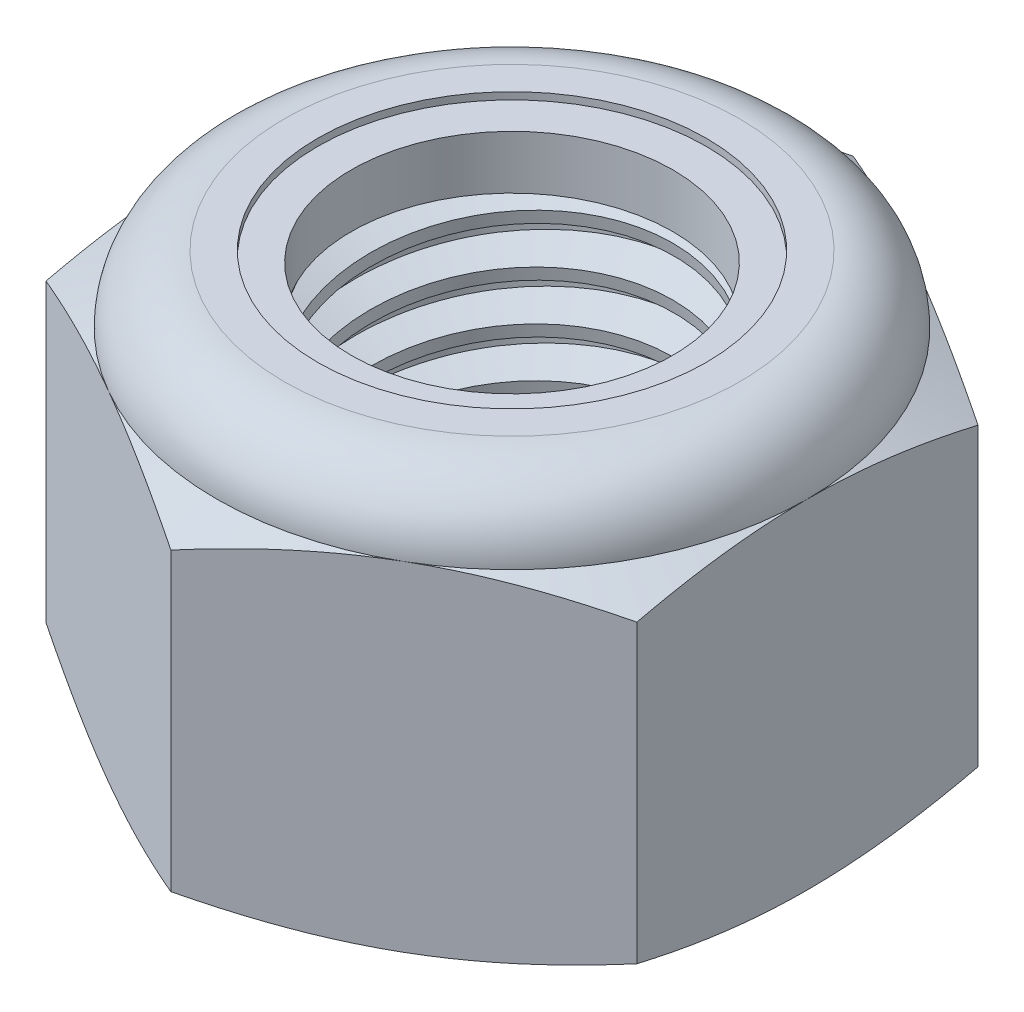
SolidWorks part; units mm, degrees
ref_plane "Front" through (0, 0, 0) normal (0, 0, 1) x (1, 0, 0)
ref_plane "Top" through (0, 0, 0) normal (0, 1, 0) x (1, 0, 0)
ref_plane "Right" through (0, 0, 0) normal (1, 0, 0) x (0, 0, -1)
sketch "Sketch1" plane through (0, 0, 0) normal (0, 1, 0) x (1, 0, 0)
  line L1 (0, 7.3323) -> (-6.35, 3.6662)
  line L2 (-6.35, 3.6662) -> (-6.35, -3.6662)
  line L3 (-6.35, -3.6662) -> (0, -7.3323)
  line L4 (0, -7.3323) -> (6.35, -3.6662)
  line L5 (6.35, -3.6662) -> (6.35, 3.6662)
  line L6 (6.35, 3.6662) -> (0, 7.3323)
  circle A0 centre (0, 0) radius 6.35 construction
  dimension "Hex Flats" = 12.7
extrude "Extrude1" add sketch "Sketch1" along normal blind 8.7312
sketch "Sketch2" plane through (0, 0, 0) normal (1, 0, 0) x (0, 0, -1)
  line L0 (-3.9624, 0) -> (-3.9624, 8.7312) construction
  line L1 (0, 0) -> (3.9624, 0)
  line L2 (0, 0) -> (0, 8.7312)
  line L3 (0, 8.7312) -> (3.9624, 8.7312)
  line L4 (3.9624, 0) -> (3.9624, 8.7312)
  line L5 (-3.6662, 8.7312) -> (3.6662, 8.7312) construction
  line L7 (0, -3.9624) -> (0, 0) construction
  dimension "Thread Dia" = 7.9248
revolve "Revolve1" add sketch "Sketch2" angle 360 about L7
sketch "Sketch3" plane through (0, 0, 0) normal (1, 0, 0) x (0, 0, -1)
  line L0 (3.9624, 8.7312) -> (-3.9624, 8.7312) construction
  line L1 (-3.9624, 8.7312) -> (-3.9624, 7.6729) construction
  line L2 (-3.9624, 7.6729) -> (3.9624, 8.7312) construction
  line L3 (3.9624, 8.7312) -> (3.9799, 8.6001) construction
  line L4 (3.9799, 8.6001) -> (4.1025, 7.6822)
  line L5 (4.1025, 7.6822) -> (3.4909, 7.9342)
  line L6 (3.4909, 7.9342) -> (3.4559, 8.1965)
  line L7 (3.4559, 8.1965) -> (3.9799, 8.6001)
  line L8 (3.4734, 8.0653) -> (4.0412, 8.1412) construction
  line L9 (3.9624, 8.7312) -> (3.9624, 8.1307) construction
  line L10 (3.9624, 8.1307) -> (-3.9624, 7.0723) construction
  line L11 (-3.9624, 7.0723) -> (-3.9624, 7.6729) construction
  line L12 (-0.1509, 8.7312) -> (0.1509, 6.4717) construction
  line L13 (-3.9624, 0) -> (-3.9624, 8.7312) construction
  line L14 (0, 8.7312) -> (3.9624, 8.7312) construction
  line L15 (3.9624, 0) -> (3.9624, 8.7312) construction
  point P13 (0, 7.6015)
  dimension "D1" = 0.1323
  dimension "D2" = 0.2646
  dimension "Thread Pitch" = 1.0583
  dimension "D4" = 60
  dimension "D5" = 1.0583
revolve "Cut-Revolve1" cut sketch "Sketch3" angle 360 about L12
pattern_linear "LPattern1" count 8 spacing 1.0583 along (0, -1, 0) count 2 spacing 1.0583 along (0, 1, 0) of "Cut-Revolve1"
sketch "Sketch4" plane through (0, 0, 0) normal (1, 0, 0) x (0, 0, -1)
  line L0 (0, 8.7312) -> (3.9624, 8.7312)
  line L1 (3.9624, 8.7312) -> (3.4559, 8.4951)
  line L2 (3.4559, 8.4951) -> (3.4559, 0.2362)
  line L3 (3.4559, 0.2362) -> (3.9624, 0)
  line L4 (3.9624, 0) -> (0, 0)
  line L5 (0, 0) -> (0, 8.7312)
  line L6 (3.9624, 0) -> (3.9624, 8.7312) construction
  line L7 (0, 8.7312) -> (3.9624, 8.7312) construction
  line L8 (0, 0) -> (3.9624, 0) construction
  line L9 (0, 0) -> (0, 8.7312) construction
  line L10 (0, 8.7312) -> (0, 9.2901) construction
  dimension "D1" = 25
revolve "Cut-Revolve2" cut sketch "Sketch4" angle 360 about L10
combine bodies "Combine1" operation type subtract main body 112 bodies to subtract 111
sketch "Sketch5" plane through (0, 0, 0) normal (1, 0, 0) x (0, 0, -1)
  line L0 (0, 0) -> (6.35, 0)
  line L1 (6.35, 0) -> (7.3323, 0.4581)
  line L2 (7.3323, 0.4581) -> (7.3323, 6.818)
  line L3 (7.3323, 6.818) -> (6.35, 7.276)
  line L4 (4.8948, 8.7312) -> (4.8948, 10.0012)
  line L5 (4.8948, 10.0012) -> (8.6023, 10.0012)
  line L6 (8.6023, 10.0012) -> (8.6023, -1.27)
  line L7 (8.6023, -1.27) -> (0, -1.27)
  line L8 (0, -1.27) -> (0, 0)
  line L9 (6.35, 7.276) -> (6.35, 0) construction
  line L10 (0, 0) -> (3.9624, 0) construction
  line L13 (7.3323, 3.638) -> (8.6023, 3.638) construction
  line L14 (7.3323, 8.7312) -> (7.3323, 0) construction
  line L15 (0, 0) -> (0, 10.0012) construction
  line L20 (0, 10.0012) -> (4.8948, 10.0012) construction
  line L22 (0, 8.7312) -> (3.9624, 8.7312) construction
  arc A0 (6.35, 7.276) -> (4.8948, 8.7312) centre (4.8948, 7.276) ccw
  dimension "D1" = 25
  dimension "D2" = 1.27
  dimension "D3" = 8.7312
  dimension "D4" = 1.4552
revolve "Cut-Revolve3" cut sketch "Sketch5" angle 360 about L15
sketch "Sketch6" plane through (0, 0, 0) normal (1, 0, 0) x (0, 0, -1)
  line L0 (0, 7.276) -> (6.1976, 7.276)
  line L1 (4.8948, 8.5788) -> (4.1753, 8.5788)
  line L2 (0, 10.0012) -> (0, 7.276)
  line L3 (4.1753, 10.0012) -> (0, 10.0012)
  line L4 (0, 10.0012) -> (4.8948, 10.0012) construction
  line L5 (0, 0) -> (0, 10.0012) construction
  line L6 (0, 10.0012) -> (0, 44.323) construction
  line L7 (4.1753, 8.5788) -> (4.1753, 10.0012)
  line L8 (4.8948, 8.7312) -> (4.8948, 8.5788) construction
  line L9 (4.1753, 8.5788) -> (3.4559, 8.5788) construction
  line L10 (3.4559, 8.5788) -> (3.4559, 8.4951) construction
  arc A0 (6.1976, 7.276) -> (4.8948, 8.5788) centre (4.8948, 7.276) ccw
  arc A1 (6.35, 7.276) -> (4.8948, 8.7312) centre (4.8948, 7.276) ccw construction
  dimension "D1" = 0.1524
revolve "Cut-Revolve4" cut sketch "Sketch6" angle 360 about L6
sketch "Sketch7" plane through (0, 0, 0) normal (1, 0, 0) x (0, 0, -1)
  line L0 (3.4559, 7.3522) -> (6.119, 7.3522)
  line L1 (4.8948, 8.5027) -> (3.4559, 8.5027)
  line L2 (3.4559, 8.5027) -> (3.4559, 7.3522)
  line L3 (3.4559, 7.3522) -> (0, 7.3522) construction
  line L4 (0, 7.3522) -> (0, 8.5027) construction
  line L5 (0, 8.5027) -> (3.4559, 8.5027) construction
  line L6 (3.4559, 7.3522) -> (3.4559, 7.276) construction
  line L7 (0, 7.276) -> (6.1976, 7.276) construction
  line L8 (4.8948, 8.5027) -> (4.8948, 8.5788) construction
  arc A0 (6.119, 7.3522) -> (4.8948, 8.5027) centre (4.8948, 7.276) ccw
  arc A2 (6.1976, 7.276) -> (4.8948, 8.5788) centre (4.8948, 7.276) ccw construction
  dimension "D1" = 0.0762
revolve "Revolve2" add sketch "Sketch7" angle 360 about L4
equation "\"D1@Sketch3\"=\"Thread Pitch@Sketch3\"/8"
equation "\"D2@Sketch3\"=\"Thread Pitch@Sketch3\"/4"
equation "\"D5@Sketch3\"=\"Thread Pitch@Sketch3\""
equation "\"D4@LPattern1\"=\"Thread Pitch@Sketch3\""
equation "\"D3@LPattern1\"=\"Thread Pitch@Sketch3\""
equation "\"D1@LPattern1\"=\"Height@Extrude1\"/\"Thread Pitch@Sketch3\""
equation "\"D4@Sketch5\"=\"Height@Extrude1\"/6"
